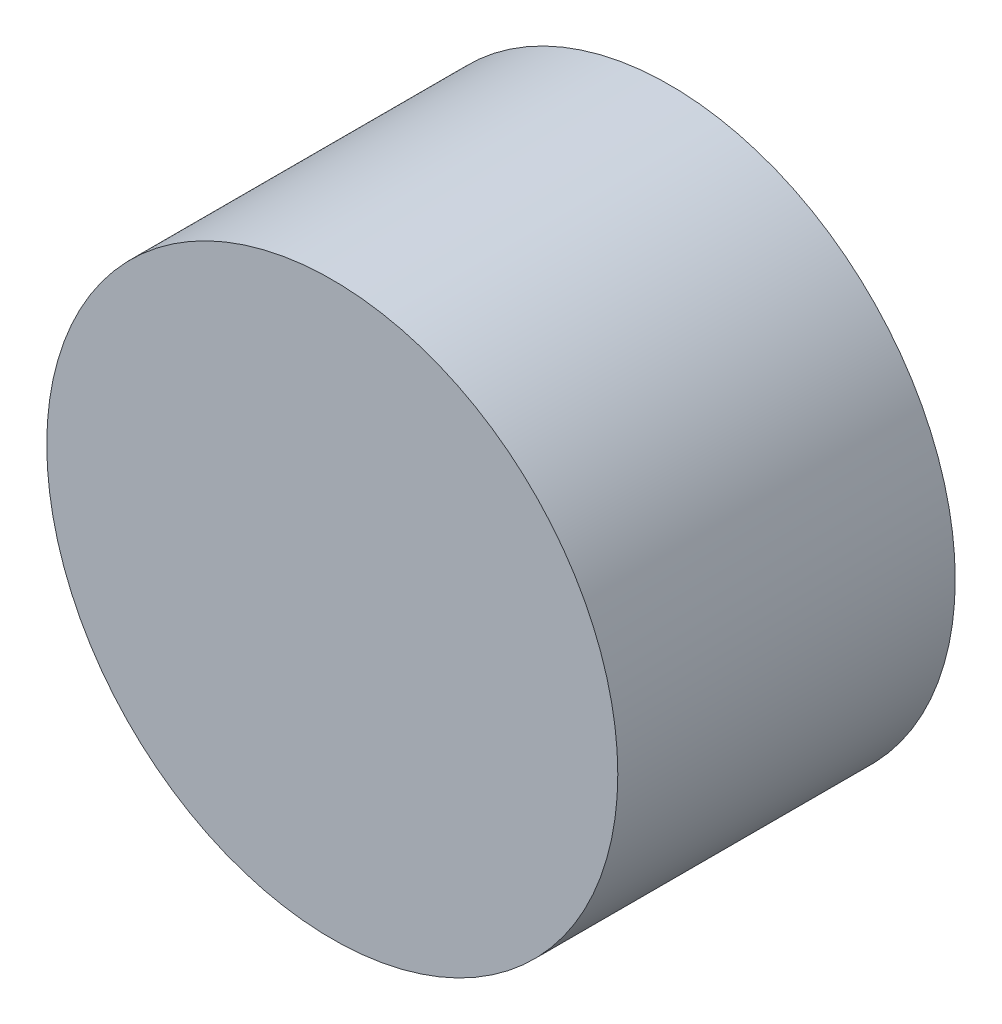
SolidWorks part; units mm, degrees
ref_plane "Front Plane" through (0, 0, 0) normal (0, 0, 1) x (1, 0, 0)
ref_plane "Top Plane" through (0, 0, 0) normal (0, 1, 0) x (1, 0, 0)
ref_plane "Right Plane" through (0, 0, 0) normal (1, 0, 0) x (0, 0, -1)
sketch "Sketch1" plane through (0, 0, 0) normal (0, 0, 1) x (1, 0, 0)
  circle A0 centre (0, 0) radius 2.75
  dimension "D1" = 5.5
extrude "Boss-Extrude1" add sketch "Sketch1" along normal blind 3.25
